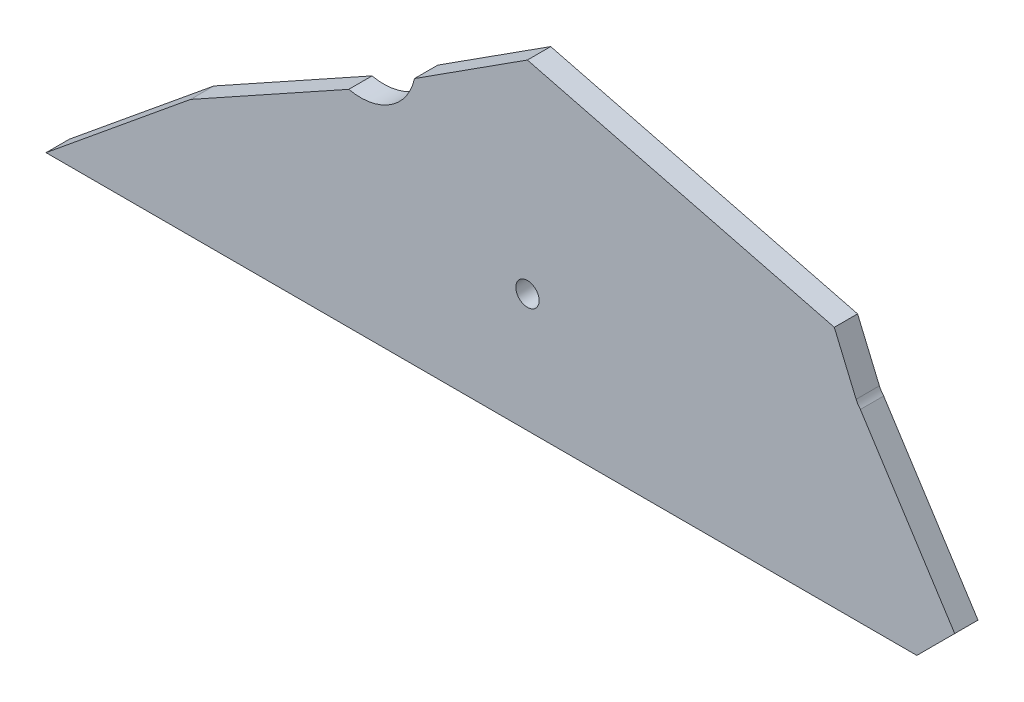
SolidWorks part; units mm, degrees
ref_plane "Front Plane" through (0, 0, 0) normal (0, 0, 1) x (1, 0, 0)
ref_plane "Top Plane" through (0, 0, 0) normal (0, 1, 0) x (1, 0, 0)
ref_plane "Right Plane" through (0, 0, 0) normal (1, 0, 0) x (0, 0, -1)
sketch "Sketch1" plane through (0, 0, 0) normal (0, 0, 1) x (1, 0, 0)
  line L0 (-201.5015, -50.8388) -> (172.4985, -50.8388)
  line L1 (172.4985, -50.8388) -> (188.762, -34.5753)
  line L2 (188.762, -34.5753) -> (148.24, 28.5355)
  line L3 (146.413, 31.381) -> (137.0473, 53.4781)
  line L4 (137.0473, 53.4781) -> (5.2397, 86.986)
  line L5 (5.2397, 86.986) -> (-43.2504, 55.8516)
  line L7 (-71.4867, 37.7217) -> (-139.4273, 0)
  line L8 (-201.5015, -50.8388) -> (-139.4273, 0)
  arc A0 (148.24, 28.5355) -> (146.413, 31.381) centre (155.6201, 35.2834) cw
  arc A1 (-43.2504, 55.8516) -> (-71.4867, 37.7217) centre (-66.4335, 60.9048) cw
  dimension "D4" = 10
  dimension "D1" = 374
  dimension "D2" = 23
  dimension "D3" = 75
  dimension "D5" = 24
  dimension "D6" = 136
extrude "Boss-Extrude1" add sketch "Sketch1" along normal blind 10
sketch "Sketch2" plane through (0, 0, 10) normal (0, 0, 1) x (1, 0, 0)
  line L0 (5.2397, -913.014) -> (5.2397, 49086.986) construction
  circle A1 centre (5.2742, 0) radius 5
  dimension "D1" = 10
extrude "Cut-Extrude1" cut sketch "Sketch2" against normal blind 10
